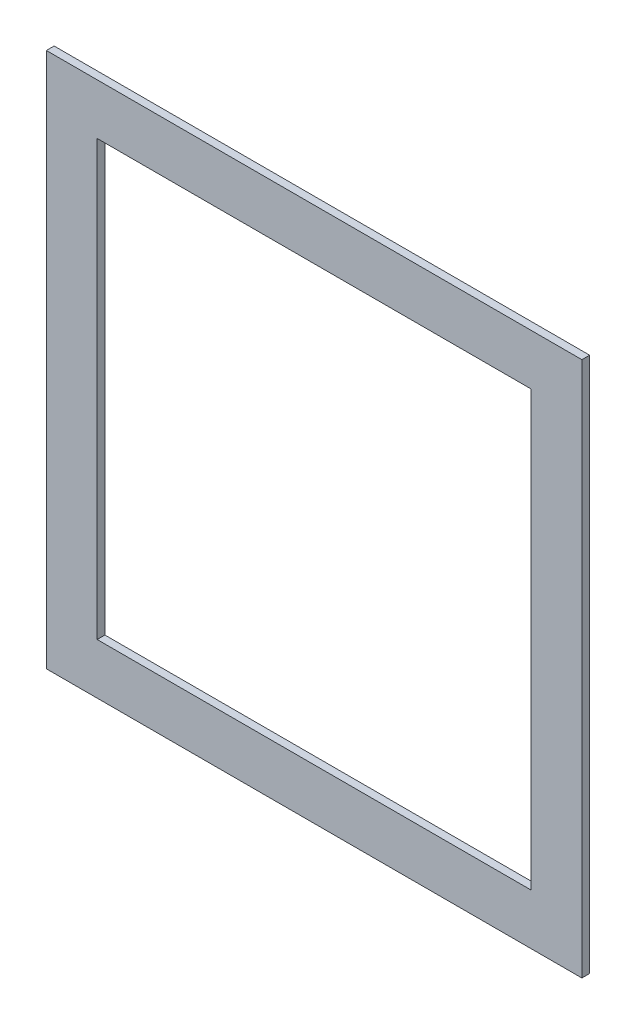
SolidWorks part; units mm, degrees
ref_plane "Front Plane" through (0, 0, 0) normal (0, 0, 1) x (1, 0, 0)
ref_plane "Top Plane" through (0, 0, 0) normal (0, 1, 0) x (1, 0, 0)
ref_plane "Right Plane" through (0, 0, 0) normal (1, 0, 0) x (0, 0, -1)
sketch "Sketch1" plane through (0, 0, 0) normal (0, 0, 1) x (1, 0, 0)
  line L1 (-149.225, 149.225) -> (149.225, 149.225)
  line L2 (-149.225, 149.225) -> (-149.225, -149.225)
  line L3 (-149.225, -149.225) -> (149.225, -149.225)
  line L4 (149.225, 149.225) -> (149.225, -149.225)
  line L5 (-149.225, 149.225) -> (149.225, -149.225) construction
  line L6 (-149.225, -149.225) -> (149.225, 149.225) construction
  line L7 (-184.15, -184.15) -> (184.15, -184.15)
  line L8 (-184.15, -184.15) -> (-184.15, 184.15)
  line L9 (-184.15, 184.15) -> (184.15, 184.15)
  line L10 (184.15, -184.15) -> (184.15, 184.15)
  line L11 (-184.15, -184.15) -> (184.15, 184.15) construction
  line L12 (-184.15, 184.15) -> (184.15, -184.15) construction
  point P4 (0, 0)
  point P5 (0, 0)
  dimension "D1" = 298.45
  dimension "D2" = 298.45
  dimension "D3" = 34.925
  dimension "D4" = 34.925
extrude "Boss-Extrude1" add sketch "Sketch1" along normal blind 5.334
